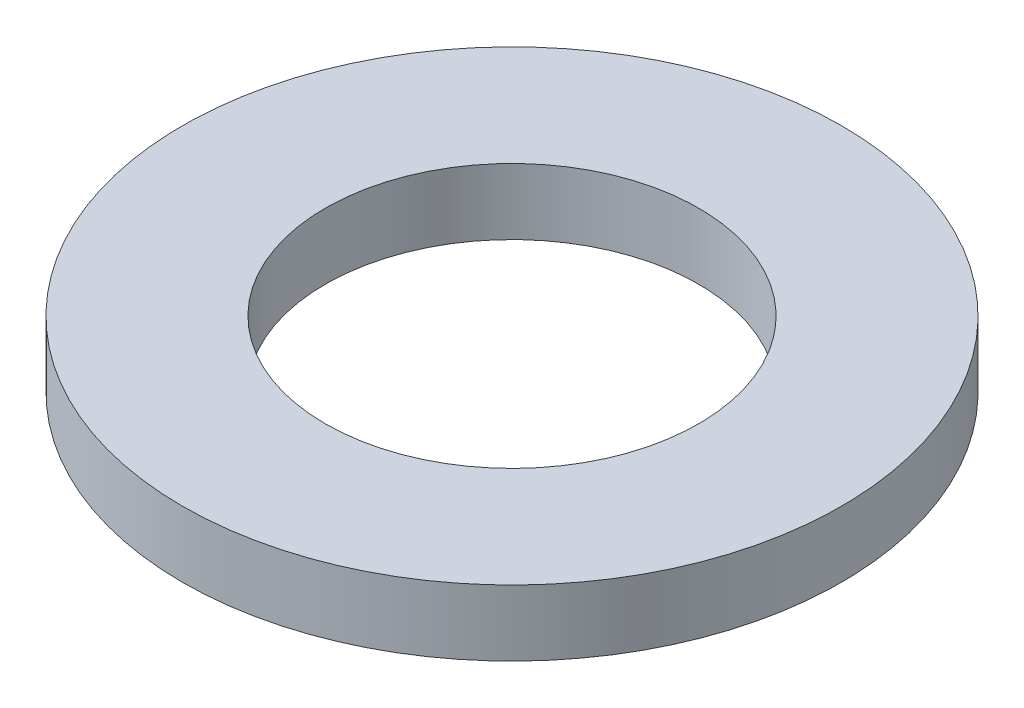
SolidWorks part; units mm, degrees
material "Plain Carbon Steel"
ref_plane "Front Plane" through (0, 0, 0) normal (0, 0, 1) x (1, 0, 0)
ref_plane "Top Plane" through (0, 0, 0) normal (0, 1, 0) x (1, 0, 0)
ref_plane "Right Plane" through (0, 0, 0) normal (1, 0, 0) x (0, 0, -1)
sketch "Sketch1" plane through (0, 0, 0) normal (0, 1, 0) x (1, 0, 0)
  circle A0 centre (0, 0) radius 15
  circle A1 centre (0, 0) radius 8.5
  dimension "D1" = 30
  dimension "D2" = 17
extrude "Boss-Extrude1" add sketch "Sketch1" along normal mid plane 3
